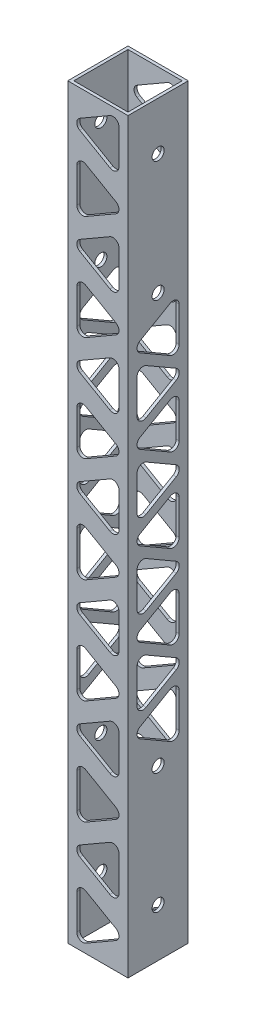
SolidWorks part; units mm, degrees
material "6061 Alloy"
ref_plane "Front Plane" through (0, 0, 0) normal (0, 0, 1) x (1, 0, 0)
ref_plane "Top Plane" through (0, 0, 0) normal (0, 1, 0) x (1, 0, 0)
ref_plane "Right Plane" through (0, 0, 0) normal (1, 0, 0) x (0, 0, -1)
sketch "Sketch1" plane through (0, 0, 0) normal (0, 1, 0) x (1, 0, 0)
  line L0 (-31.75, -31.75) -> (31.75, 31.75) construction
  line L1 (-31.75, 31.75) -> (31.75, 31.75)
  line L2 (-31.75, 31.75) -> (-31.75, -31.75)
  line L3 (-31.75, -31.75) -> (31.75, -31.75)
  line L4 (31.75, 31.75) -> (31.75, -31.75)
  line L5 (28.575, -28.575) -> (-28.575, 28.575) construction
  line L6 (-28.575, 28.575) -> (28.575, 28.575)
  line L7 (-28.575, 28.575) -> (-28.575, -28.575)
  line L8 (-28.575, -28.575) -> (28.575, -28.575)
  line L9 (28.575, 28.575) -> (28.575, -28.575)
  point P7 (0, 0)
  point P10 (0, 0)
  point P14 (0, 0)
  dimension "D1" = 63.5
  dimension "D2" = 3.175
  dimension "D3" = 3.175
  dimension "D4" = 3.175
extrude "Boss-Extrude1" add sketch "Sketch1" along normal blind 787.4
sketch "Sketch2" plane through (-31.75, 0, 0) normal (-1, 0, 0) x (0, 0, 1)
  line L0 (31.75, 393.7) -> (-31.75, 393.7) construction
  line L1 (31.75, 787.4) -> (31.75, 0) construction
  line L2 (-31.75, 787.4) -> (-31.75, 0) construction
  line L3 (0, 50.8) -> (0, 736.6) construction
  line L4 (0, 609.6) -> (0, 177.8) construction
  circle A0 centre (0, 50.8) radius 6.35
  circle A1 centre (0, 177.8) radius 6.35
  circle A2 centre (0, 609.6) radius 6.35
  circle A3 centre (0, 736.6) radius 6.35
  point P10 (0, 393.7)
  point P13 (0, 393.7)
  dimension "D3" = 12.7
extrude "Cut-Extrude1" cut sketch "Sketch2" against normal through all
sketch "Sketch3" plane through (31.75, 0, 0) normal (1, 0, 0) x (0, 0, -1)
  line L0 (31.75, 787.4) -> (31.75, 0) construction
  line L1 (-19.05, 212.0059) -> (12.7, 193.675)
  line L2 (22.225, 199.1743) -> (22.225, 235.836)
  line L3 (12.7, 241.3353) -> (-19.05, 223.0044)
  line L4 (19.05, 266.9985) -> (-12.7, 285.3294)
  line L5 (-22.225, 279.8301) -> (-22.225, 243.1684)
  line L6 (-12.7, 237.6691) -> (19.05, 256)
  line L7 (-31.75, 787.4) -> (-31.75, 0) construction
  line L8 (-19.05, 300.1033) -> (12.7, 281.7724)
  line L9 (22.225, 287.2717) -> (22.225, 323.9334)
  line L10 (12.7, 329.4327) -> (-19.05, 311.1018)
  line L11 (19.05, 355.0959) -> (-12.7, 373.4268)
  line L12 (-22.225, 367.9275) -> (-22.225, 331.2658)
  line L13 (-12.7, 325.7665) -> (19.05, 344.0974)
  line L14 (-19.05, 388.2007) -> (12.7, 369.8699)
  line L15 (22.225, 375.3691) -> (22.225, 412.0309)
  line L16 (12.7, 417.5301) -> (-19.05, 399.1993)
  line L17 (19.05, 443.1934) -> (-12.7, 461.5242)
  line L18 (-22.225, 456.025) -> (-22.225, 419.3632)
  line L19 (-12.7, 413.864) -> (19.05, 432.1948)
  line L20 (-19.05, 476.2982) -> (12.7, 457.9673)
  line L21 (22.225, 463.4666) -> (22.225, 500.1283)
  line L22 (12.7, 505.6276) -> (-19.05, 487.2967)
  line L23 (19.05, 531.2908) -> (-12.7, 549.6217)
  line L24 (-22.225, 544.1224) -> (-22.225, 507.4607)
  line L25 (-12.7, 501.9614) -> (19.05, 520.2923)
  line L26 (-19.05, 564.3956) -> (12.7, 546.0647)
  line L27 (22.225, 551.564) -> (22.225, 588.2257)
  line L28 (12.7, 593.725) -> (-19.05, 575.3941)
  line L32 (-12.7, 590.0588) -> (19.05, 608.3897) [skipped]
  line L33 (-22.225, 632.2198) -> (-22.225, 595.5581) [skipped]
  line L34 (19.05, 619.3882) -> (-12.7, 637.7191) [skipped]
  circle A0 centre (5.2917, 217.5051) radius 16.9333 construction
  circle A1 centre (-5.2917, 261.4992) radius 16.9333 construction
  arc A2 (-12.7, 285.3294) -> (-22.225, 279.8301) centre (-15.875, 279.8301) ccw
  arc A3 (-22.225, 243.1684) -> (-12.7, 237.6691) centre (-15.875, 243.1684) ccw
  arc A4 (19.05, 266.9985) -> (19.05, 256) centre (15.875, 261.4992) cw
  arc A5 (22.225, 235.836) -> (12.7, 241.3353) centre (15.875, 235.836) ccw
  arc A6 (12.7, 193.675) -> (22.225, 199.1743) centre (15.875, 199.1743) ccw
  arc A7 (-19.05, 212.0059) -> (-19.05, 223.0044) centre (-15.875, 217.5051) cw
  circle A8 centre (0, 177.8) radius 6.35 construction
  arc A9 (-19.05, 300.1033) -> (-19.05, 311.1018) centre (-15.875, 305.6026) cw
  arc A10 (12.7, 281.7724) -> (22.225, 287.2717) centre (15.875, 287.2717) ccw
  arc A11 (22.225, 323.9334) -> (12.7, 329.4327) centre (15.875, 323.9334) ccw
  arc A12 (19.05, 355.0959) -> (19.05, 344.0974) centre (15.875, 349.5967) cw
  arc A13 (-12.7, 373.4268) -> (-22.225, 367.9275) centre (-15.875, 367.9275) ccw
  arc A14 (-22.225, 331.2658) -> (-12.7, 325.7665) centre (-15.875, 331.2658) ccw
  arc A15 (-19.05, 388.2007) -> (-19.05, 399.1993) centre (-15.875, 393.7) cw
  arc A16 (12.7, 369.8699) -> (22.225, 375.3691) centre (15.875, 375.3691) ccw
  arc A17 (22.225, 412.0309) -> (12.7, 417.5301) centre (15.875, 412.0309) ccw
  arc A18 (19.05, 443.1934) -> (19.05, 432.1948) centre (15.875, 437.6941) cw
  arc A19 (-12.7, 461.5242) -> (-22.225, 456.025) centre (-15.875, 456.025) ccw
  arc A20 (-22.225, 419.3632) -> (-12.7, 413.864) centre (-15.875, 419.3632) ccw
  arc A21 (-19.05, 476.2982) -> (-19.05, 487.2967) centre (-15.875, 481.7974) cw
  arc A22 (12.7, 457.9673) -> (22.225, 463.4666) centre (15.875, 463.4666) ccw
  arc A23 (22.225, 500.1283) -> (12.7, 505.6276) centre (15.875, 500.1283) ccw
  arc A24 (19.05, 531.2908) -> (19.05, 520.2923) centre (15.875, 525.7915) cw
  arc A25 (-12.7, 549.6217) -> (-22.225, 544.1224) centre (-15.875, 544.1224) ccw
  arc A26 (-22.225, 507.4607) -> (-12.7, 501.9614) centre (-15.875, 507.4607) ccw
  arc A27 (-19.05, 564.3956) -> (-19.05, 575.3941) centre (-15.875, 569.8949) cw
  arc A28 (12.7, 546.0647) -> (22.225, 551.564) centre (15.875, 551.564) ccw
  arc A29 (22.225, 588.2257) -> (12.7, 593.725) centre (15.875, 588.2257) ccw
  circle A33 centre (0, 609.6) radius 6.35 construction
  arc A34 (-22.225, 595.5581) -> (-12.7, 590.0588) centre (-15.875, 595.5581) ccw [skipped]
  arc A35 (-12.7, 637.7191) -> (-22.225, 632.2198) centre (-15.875, 632.2198) ccw [skipped]
  arc A36 (19.05, 619.3882) -> (19.05, 608.3897) centre (15.875, 613.889) cw [skipped]
  point P24 (-22.225, 217.5051)
  point P27 (22.225, 261.4992)
  dimension "D1" = 6.35
  dimension "D7" = 15.875
  dimension "D2" = 9.525
  dimension "D3" = 9.525
  dimension "D4" = 9.525
  dimension "D5" = 9.525
  dimension "D6" = 9.525
  dimension "D9" = 15.875
  dimension "D8" = 5
extrude "Cut-Extrude2" cut sketch "Sketch3" against normal blind 71.12
sketch "Sketch5" plane through (0, 0, -31.75) normal (0, 0, -1) x (-1, 0, 0)
  line L1 (19.05, 759.5441) -> (-12.7, 777.875)
  line L2 (-22.225, 772.3757) -> (-22.225, 735.714)
  line L3 (-12.7, 730.2147) -> (19.05, 748.5456)
  line L4 (-19.05, 691.3603) -> (12.7, 673.0295)
  line L5 (22.225, 678.5287) -> (22.225, 715.1905)
  line L6 (12.7, 720.6897) -> (-19.05, 702.3589)
  line L7 (-31.75, 787.4) -> (-31.75, 0) construction
  line L8 (-31.75, 787.4) -> (31.75, 787.4) construction
  line L9 (31.75, 787.4) -> (31.75, 0) construction
  line L10 (19.05, 648.9601) -> (-12.7, 667.2909)
  line L11 (-22.225, 661.7917) -> (-22.225, 625.1299)
  line L12 (-12.7, 619.6307) -> (19.05, 637.9615)
  line L13 (-19.05, 580.7763) -> (12.7, 562.4454)
  line L14 (22.225, 567.9447) -> (22.225, 604.6064)
  line L15 (12.7, 610.1057) -> (-19.05, 591.7748)
  line L16 (19.05, 538.376) -> (-12.7, 556.7068)
  line L17 (-22.225, 551.2076) -> (-22.225, 514.5458)
  line L18 (-12.7, 509.0466) -> (19.05, 527.3774)
  line L19 (-19.05, 470.1922) -> (12.7, 451.8613)
  line L20 (22.225, 457.3606) -> (22.225, 494.0223)
  line L21 (12.7, 499.5216) -> (-19.05, 481.1907)
  line L22 (19.05, 427.7919) -> (-12.7, 446.1228)
  line L23 (-22.225, 440.6235) -> (-22.225, 403.9618)
  line L24 (-12.7, 398.4625) -> (19.05, 416.7934)
  line L25 (-19.05, 359.6081) -> (12.7, 341.2772)
  line L26 (22.225, 346.7765) -> (22.225, 383.4382)
  line L27 (12.7, 388.9375) -> (-19.05, 370.6066)
  line L28 (19.05, 317.2078) -> (-12.7, 335.5387)
  line L29 (-22.225, 330.0394) -> (-22.225, 293.3777)
  line L30 (-12.7, 287.8784) -> (19.05, 306.2093)
  line L31 (-19.05, 249.024) -> (12.7, 230.6932)
  line L32 (22.225, 236.1924) -> (22.225, 272.8542)
  line L33 (12.7, 278.3534) -> (-19.05, 260.0226)
  line L34 (19.05, 206.6237) -> (-12.7, 224.9546)
  line L35 (-22.225, 219.4553) -> (-22.225, 182.7936)
  line L36 (-12.7, 177.2943) -> (19.05, 195.6252)
  line L37 (-19.05, 138.4399) -> (12.7, 120.1091)
  line L38 (22.225, 125.6083) -> (22.225, 162.2701)
  line L39 (12.7, 167.7693) -> (-19.05, 149.4385)
  line L40 (19.05, 96.0397) -> (-12.7, 114.3705)
  line L41 (-22.225, 108.8713) -> (-22.225, 72.2095)
  line L42 (-12.7, 66.7103) -> (19.05, 85.0411)
  line L43 (-19.05, 27.8559) -> (12.7, 9.525)
  line L44 (22.225, 15.0243) -> (22.225, 51.686)
  line L45 (12.7, 57.1853) -> (-19.05, 38.8544)
  line L46 (-31.75, 0) -> (31.75, 0) construction
  circle A0 centre (-5.2917, 754.0449) radius 16.9333 construction
  circle A1 centre (5.2917, 696.8596) radius 16.9333 construction
  arc A2 (22.225, 715.1905) -> (12.7, 720.6897) centre (15.875, 715.1905) ccw
  arc A3 (12.7, 673.0295) -> (22.225, 678.5287) centre (15.875, 678.5287) ccw
  arc A4 (-19.05, 691.3603) -> (-19.05, 702.3589) centre (-15.875, 696.8596) cw
  arc A5 (-22.225, 735.714) -> (-12.7, 730.2147) centre (-15.875, 735.714) ccw
  arc A6 (-12.7, 777.875) -> (-22.225, 772.3757) centre (-15.875, 772.3757) ccw
  arc A7 (19.05, 759.5441) -> (19.05, 748.5456) centre (15.875, 754.0449) cw
  arc A8 (19.05, 648.9601) -> (19.05, 637.9615) centre (15.875, 643.4608) cw
  arc A9 (-12.7, 667.2909) -> (-22.225, 661.7917) centre (-15.875, 661.7917) ccw
  arc A10 (-22.225, 625.1299) -> (-12.7, 619.6307) centre (-15.875, 625.1299) ccw
  arc A11 (-19.05, 580.7763) -> (-19.05, 591.7748) centre (-15.875, 586.2755) cw
  arc A12 (12.7, 562.4454) -> (22.225, 567.9447) centre (15.875, 567.9447) ccw
  arc A13 (22.225, 604.6064) -> (12.7, 610.1057) centre (15.875, 604.6064) ccw
  arc A14 (19.05, 538.376) -> (19.05, 527.3774) centre (15.875, 532.8767) cw
  arc A15 (-12.7, 556.7068) -> (-22.225, 551.2076) centre (-15.875, 551.2076) ccw
  arc A16 (-22.225, 514.5458) -> (-12.7, 509.0466) centre (-15.875, 514.5458) ccw
  arc A17 (-19.05, 470.1922) -> (-19.05, 481.1907) centre (-15.875, 475.6914) cw
  arc A18 (12.7, 451.8613) -> (22.225, 457.3606) centre (15.875, 457.3606) ccw
  arc A19 (22.225, 494.0223) -> (12.7, 499.5216) centre (15.875, 494.0223) ccw
  arc A20 (19.05, 427.7919) -> (19.05, 416.7934) centre (15.875, 422.2926) cw
  arc A21 (-12.7, 446.1228) -> (-22.225, 440.6235) centre (-15.875, 440.6235) ccw
  arc A22 (-22.225, 403.9618) -> (-12.7, 398.4625) centre (-15.875, 403.9618) ccw
  arc A23 (-19.05, 359.6081) -> (-19.05, 370.6066) centre (-15.875, 365.1074) cw
  arc A24 (12.7, 341.2772) -> (22.225, 346.7765) centre (15.875, 346.7765) ccw
  arc A25 (22.225, 383.4382) -> (12.7, 388.9375) centre (15.875, 383.4382) ccw
  arc A26 (19.05, 317.2078) -> (19.05, 306.2093) centre (15.875, 311.7086) cw
  arc A27 (-12.7, 335.5387) -> (-22.225, 330.0394) centre (-15.875, 330.0394) ccw
  arc A28 (-22.225, 293.3777) -> (-12.7, 287.8784) centre (-15.875, 293.3777) ccw
  arc A29 (-19.05, 249.024) -> (-19.05, 260.0226) centre (-15.875, 254.5233) cw
  arc A30 (12.7, 230.6932) -> (22.225, 236.1924) centre (15.875, 236.1924) ccw
  arc A31 (22.225, 272.8542) -> (12.7, 278.3534) centre (15.875, 272.8542) ccw
  arc A32 (19.05, 206.6237) -> (19.05, 195.6252) centre (15.875, 201.1245) cw
  arc A33 (-12.7, 224.9546) -> (-22.225, 219.4553) centre (-15.875, 219.4553) ccw
  arc A34 (-22.225, 182.7936) -> (-12.7, 177.2943) centre (-15.875, 182.7936) ccw
  arc A35 (-19.05, 138.4399) -> (-19.05, 149.4385) centre (-15.875, 143.9392) cw
  arc A36 (12.7, 120.1091) -> (22.225, 125.6083) centre (15.875, 125.6083) ccw
  arc A37 (22.225, 162.2701) -> (12.7, 167.7693) centre (15.875, 162.2701) ccw
  arc A38 (19.05, 96.0397) -> (19.05, 85.0411) centre (15.875, 90.5404) cw
  arc A39 (-12.7, 114.3705) -> (-22.225, 108.8713) centre (-15.875, 108.8713) ccw
  arc A40 (-22.225, 72.2095) -> (-12.7, 66.7103) centre (-15.875, 72.2095) ccw
  arc A41 (-19.05, 27.8559) -> (-19.05, 38.8544) centre (-15.875, 33.3551) cw
  arc A42 (12.7, 9.525) -> (22.225, 15.0243) centre (15.875, 15.0243) ccw
  arc A43 (22.225, 51.686) -> (12.7, 57.1853) centre (15.875, 51.686) ccw
  point P22 (22.225, 754.0449)
  point P30 (-22.225, 696.8596)
  dimension "D1" = 6.35
  dimension "D2" = 9.525
  dimension "D3" = 9.525
  dimension "D4" = 9.525
  dimension "D5" = 9.525
  dimension "D6" = 9.525
  dimension "D7" = 9.525
  dimension "D9" = 9.525
  dimension "D8" = 7
extrude "Cut-Extrude3" cut sketch "Sketch5" against normal blind 71.12
equation "\"D1@Boss-Extrude1\"=\"HoleDist\"+4"
